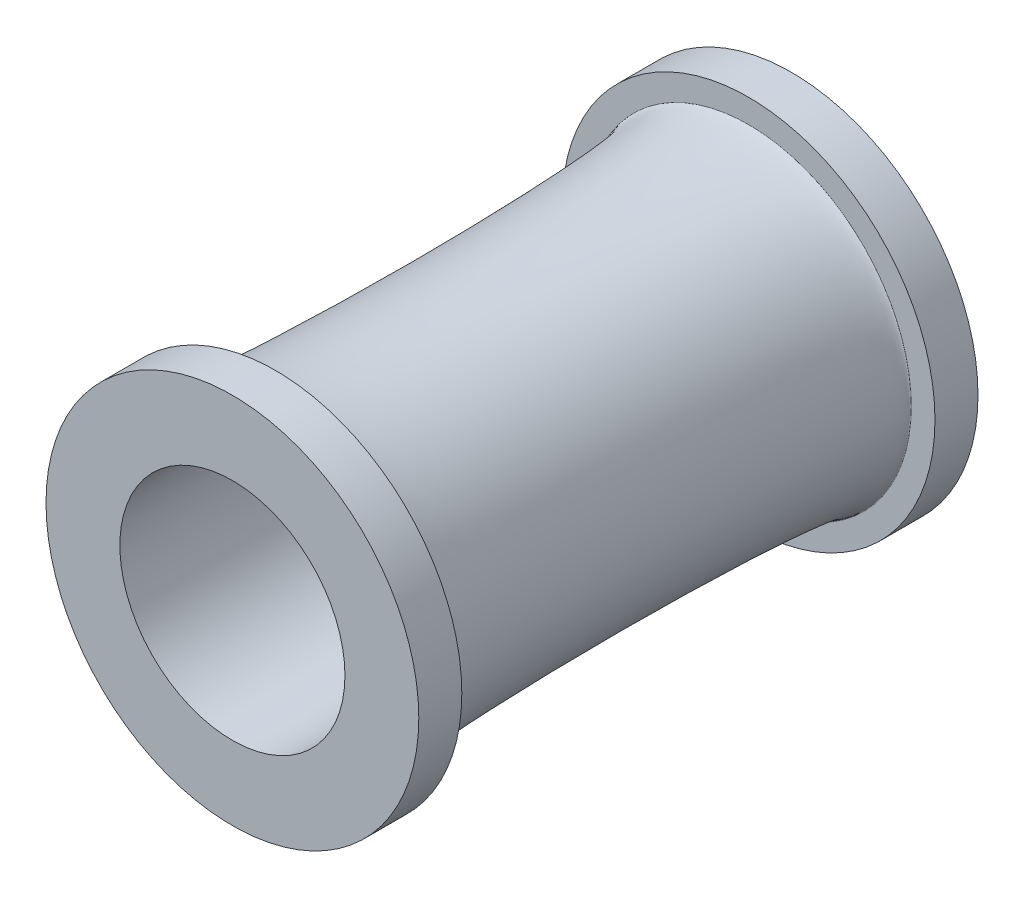
SolidWorks part; units mm, degrees
ref_plane "Front Plane" through (0, 0, 0) normal (0, 0, 1) x (1, 0, 0)
ref_plane "Top Plane" through (0, 0, 0) normal (0, 1, 0) x (1, 0, 0)
ref_plane "Right Plane" through (0, 0, 0) normal (1, 0, 0) x (0, 0, -1)
sketch "Sketch1" plane through (0, 0, 0) normal (0, 0, 1) x (1, 0, 0)
  circle A0 centre (0, 0) radius 9.9695
  circle A1 centre (0, 0) radius 14.4145
  dimension "D1" = 19.939
  dimension "D2" = 28.829
extrude "Boss-Extrude1" add sketch "Sketch1" along normal blind 41.91
ref_plane "Plane1" through (0, 0, 20.955) normal (0, 0, 1) x (1, 0, 0)
sketch "Sketch2" plane through (0, 0, 41.91) normal (0, 0, 1) x (1, 0, 0)
  circle A0 centre (0, 0) radius 9.9695 construction
  circle A1 centre (0, 0) radius 9.9695
  circle A2 centre (0, 0) radius 19.05
  dimension "D1" = 38.1
extrude "Boss-Extrude2" add sketch "Sketch2" along normal blind 3.81
mirror "Mirror1" about plane through (0, 0, 20.955) normal (0, 0, 1) of "Boss-Extrude2"
fillet "Fillet1" radius 1.778 2 edges at (19.05, 0, 41.91) (19.05, 0, 0)
ref_axis "Axis1" through (0, 0, 45.72) along (0, 0, -1)
sketch "Sketch3" plane through (0, 0, 0) normal (0, 1, 0) x (1, 0, 0)
  line L0 (-14.4145, 0) -> (-14.4145, -41.91) construction
  ellipse E0 centre (-14.4145, -20.955) end of major axis (-14.4145, -41.91) minor radius 1.1359
revolve "Cut-Revolve1" cut sketch "Sketch3" angle 360 about axis through (0, 0, 45.72) along (0, 0, -1)
sketch "Sketch4" plane through (0, 0, -3.81) normal (0, 0, -1) x (-1, 0, 0)
  circle A0 centre (0, 0) radius 19.05 construction
  circle A1 centre (0, 0) radius 19.05
  circle A2 centre (0, 0) radius 16.51
  dimension "D1" = 2.54
extrude "Rim_Cut" cut sketch "Sketch4" against normal through all
